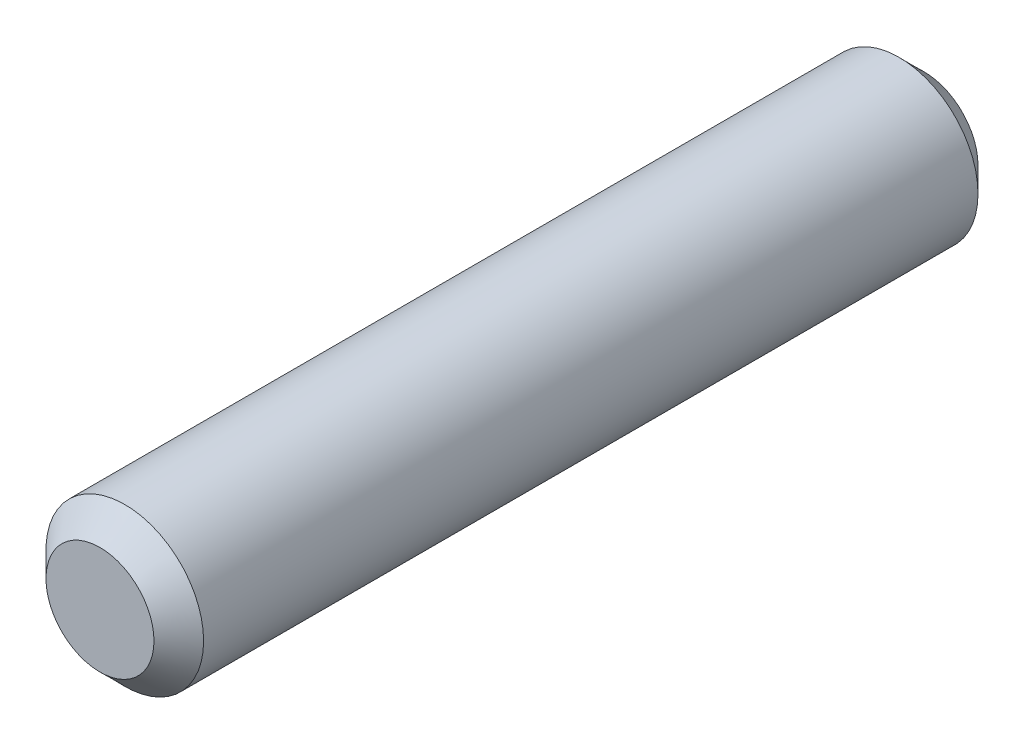
SolidWorks part; units mm, degrees
material "Alloy Steel"
ref_plane "Front Plane" through (0, 0, 0) normal (0, 0, 1) x (1, 0, 0)
ref_plane "Top Plane" through (0, 0, 0) normal (0, 1, 0) x (1, 0, 0)
ref_plane "Right Plane" through (0, 0, 0) normal (1, 0, 0) x (0, 0, -1)
sketch "Sketch1" plane through (0, 0, 0) normal (0, 0, 1) x (1, 0, 0)
  circle A0 centre (0, 0) radius 3.175
  dimension "D1" = 6.35
extrude "Boss-Extrude1" add sketch "Sketch1" along normal blind 33.2
chamfer "Chamfer1" distance 1 angle 45 2 edges at (3.175, 0, 33.2) (3.175, 0, 0)
